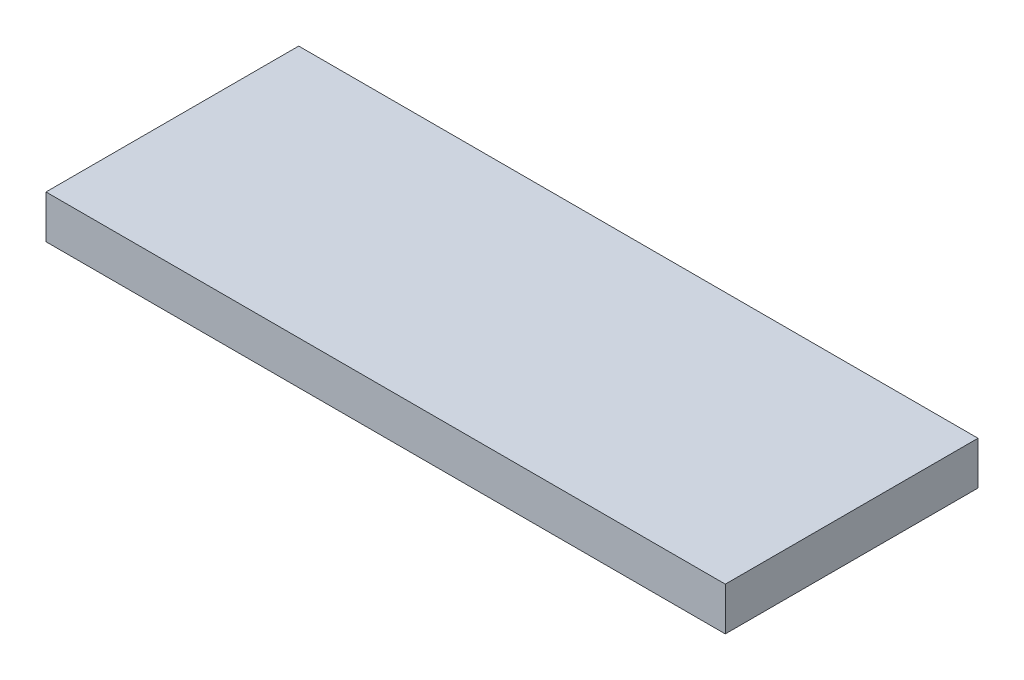
SolidWorks part; units mm, degrees
ref_plane "Front Plane" through (0, 0, 0) normal (0, 0, 1) x (1, 0, 0)
ref_plane "Top Plane" through (0, 0, 0) normal (0, 1, 0) x (1, 0, 0)
ref_plane "Right Plane" through (0, 0, 0) normal (1, 0, 0) x (0, 0, -1)
sketch "Sketch1" plane through (0, 0, 0) normal (0, 1, 0) x (1, 0, 0)
  line L1 (0, 0) -> (50, 0)
  line L2 (0, 0) -> (0, 18.6)
  line L3 (0, 18.6) -> (50, 18.6)
  line L4 (50, 0) -> (50, 18.6)
  dimension "D1" = 50
  dimension "D2" = 18.6
extrude "Boss-Extrude1" add sketch "Sketch1" along normal blind 3.175 contours L1 L4 L3 L2
